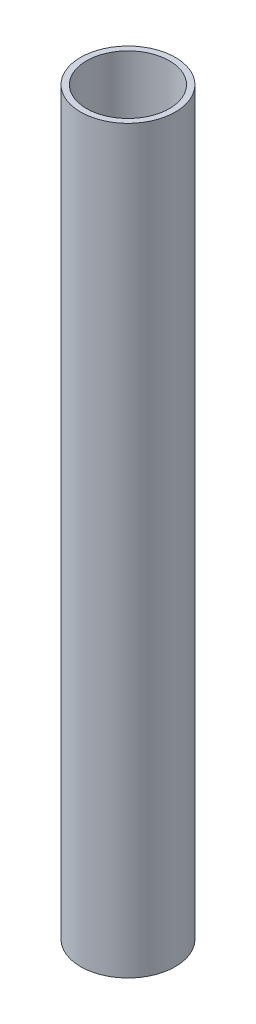
SolidWorks part; units mm, degrees
material "Hexcel AS4C (3000 丝)"
ref_plane "前视基准面" through (0, 0, 0) normal (0, 0, 1) x (1, 0, 0)
ref_plane "上视基准面" through (0, 0, 0) normal (0, 1, 0) x (1, 0, 0)
ref_plane "右视基准面" through (0, 0, 0) normal (1, 0, 0) x (0, 0, -1)
other "Configuration Table"
sketch "草图1" plane through (0, 0, 0) normal (0, 1, 0) x (1, 0, 0)
  circle A0 centre (0, 0) radius 8
  circle A1 centre (0, 0) radius 7
  dimension "D1" = 16
  dimension "D2" = 1
extrude "凸台-拉伸1" add sketch "草图1" along normal blind 125
